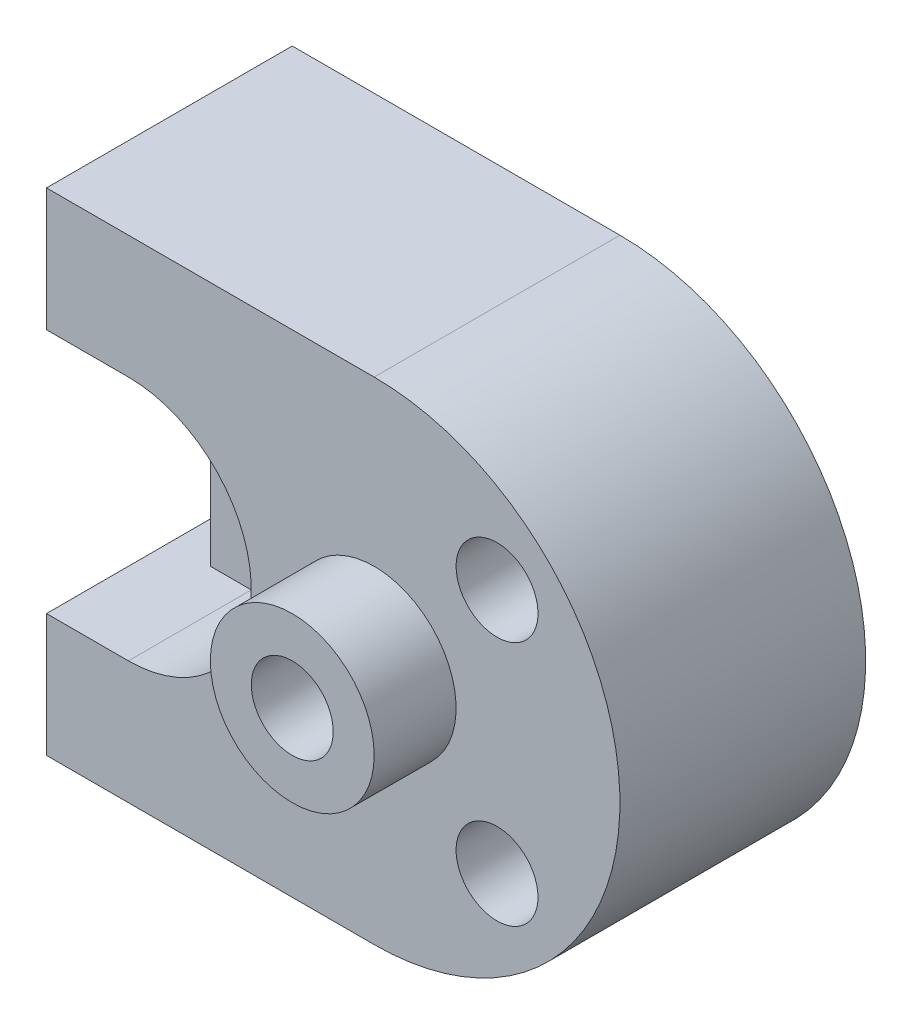
SolidWorks part; units mm, degrees
ref_plane "Front Plane" through (0, 0, 0) normal (0, 0, 1) x (1, 0, 0)
ref_plane "Top Plane" through (0, 0, 0) normal (0, 1, 0) x (1, 0, 0)
ref_plane "Right Plane" through (0, 0, 0) normal (1, 0, 0) x (0, 0, -1)
sketch "Sketch1" plane through (0, 0, 0) normal (0, 0, 1) x (1, 0, 0)
  line L1 (0, 0) -> (140, 0)
  line L2 (0, 0) -> (0, 120)
  line L3 (0, 120) -> (140, 120)
  line L4 (140, 0) -> (140, 120)
  dimension "D1" = 140
  dimension "D2" = 120
extrude "Boss-Extrude1" add sketch "Sketch1" along normal blind 60
sketch "Sketch2" plane through (0, 0, 60) normal (0, 0, 1) x (1, 0, 0)
  line L0 (0, 120) -> (0, 0) construction
  line L1 (0, 90) -> (10, 90)
  line L2 (0, 90) -> (0, 30)
  line L3 (0, 30) -> (10, 30)
  line L4 (10, 90) -> (10, 30)
  line L5 (140, 120) -> (0, 120) construction
  line L6 (80, 120) -> (140, 120)
  line L7 (140, 120) -> (140, 0)
  line L8 (140, 0) -> (80, 0)
  arc A0 (80, 120) -> (80, 0) centre (80, 60) cw
  line M2 (0, 0) -> (140, 0)
  line M3 (140, 0) -> (140, 120)
  line M4 (140, 120) -> (0, 120)
  dimension "D4" = 60
  dimension "D1" = 10
  dimension "D2" = 30
  dimension "D3" = 30
  dimension "D5" = 60
  dimension "D6" = 60
extrude "Cut-Extrude1" cut sketch "Sketch2" against normal blind 60 contours A0 L7 M4 | A0 M3 M2 | L2 L3 L4 L1
ref_plane "Plane1" through (0, 0, 30) normal (0, 0, 1) x (1, 0, 0)
sketch "Sketch3" plane through (0, 0, 30) normal (0, 0, 1) x (1, 0, 0)
  line L0 (10, 90) -> (20, 90)
  line L1 (10, 30) -> (20, 30)
  line L2 (10, 90) -> (10, 30)
  arc A0 (20, 90) -> (20, 30) centre (20, 60) cw
  dimension "D1" = 30
  dimension "D2" = 10
  dimension "D3" = 10
  dimension "D4" = 0
  dimension "D5" = 0
  dimension "D6" = 0
  dimension "D7" = 0
extrude "Cut-Extrude2" cut sketch "Sketch3" along normal blind 60 contours A0 L0 L2 L1
sketch "Sketch4" plane through (0, 0, 30) normal (0, 0, 1) x (1, 0, 0)
  line L0 (0, 30) -> (20, 30) construction
  circle A0 centre (30, 60) radius 10
  point P2 (10, 30)
  dimension "D1" = 20
  dimension "D2" = 30
  dimension "D3" = 20
extrude "Cut-Extrude3" cut sketch "Sketch4" against normal blind 60
ref_plane "Plane2" through (0, 0, 20) normal (0, 0, 1) x (1, 0, 0)
sketch "Sketch5" plane through (0, 0, 20) normal (0, 0, 1) x (1, 0, 0)
  circle A0 centre (110, 90) radius 10
  dimension "D1" = 20
  dimension "D2" = 30
  dimension "D3" = 30
extrude "Cut-Extrude4" cut sketch "Sketch5" against normal blind 60
ref_plane "Plane3" through (0, 0, 40) normal (0, 0, 1) x (1, 0, 0)
sketch "Sketch6" plane through (0, 0, 40) normal (0, 0, 1) x (1, 0, 0)
  circle A0 centre (110, 90) radius 10
  dimension "D1" = 20
  dimension "D2" = 30
  dimension "D3" = 30
extrude "Cut-Extrude5" cut sketch "Sketch6" along normal blind 60
sketch "Sketch7" plane through (0, 0, 40) normal (0, 0, 1) x (1, 0, 0)
  circle A0 centre (110, 90) radius 5
  dimension "D1" = 10
extrude "Cut-Extrude6" cut sketch "Sketch7" against normal blind 60
sketch "Sketch8" plane through (0, 0, 60) normal (0, 0, 1) x (1, 0, 0)
  circle A0 centre (110, 30) radius 10
  dimension "D1" = 20
  dimension "D3" = 30
  dimension "D2" = 30
extrude "Cut-Extrude7" cut sketch "Sketch8" against normal blind 20
sketch "Sketch9" plane through (0, 0, 40) normal (0, 0, 1) x (1, 0, 0)
  circle A0 centre (110, 30) radius 5
  dimension "D1" = 10
extrude "Cut-Extrude8" cut sketch "Sketch9" against normal blind 47
sketch "Sketch10" plane through (0, 0, 0) normal (0, 0, -1) x (-1, 0, 0)
  circle A0 centre (-110, 30) radius 10
  dimension "D1" = 20
extrude "Cut-Extrude9" cut sketch "Sketch10" against normal blind 20
sketch "Sketch11" plane through (0, 0, 60) normal (0, 0, 1) x (1, 0, 0)
  circle A0 centre (80, 60) radius 20
  circle A1 centre (30, 60) radius 10 construction
  dimension "D1" = 40
  dimension "D2" = 80
  dimension "D3" = 0
extrude "Boss-Extrude2" add sketch "Sketch11" along normal blind 20
sketch "Sketch12" plane through (0, 0, 80) normal (0, 0, 1) x (1, 0, 0)
  point P0 (80, 60)
hole_wizard "Ø20.0mm Dowel Hole1" positions "3DSketch1" profile "Sketch13" hole size "Ø20.0" standard "ISO"
sketch3d "3DSketch1"
  point P0 (80, 60, 80)
sketch "Sketch13" plane through (80, 60, 80) normal (1, 0, 0) x (0, -1, 0)
  line L0 (0, 0) -> (0, 36.0086)
  line L1 (0, 36.0086) -> (10, 30)
  line L2 (10, 30) -> (10, 0)
  line L5 (10, 0) -> (0, 0)
  line L10 (0, 36.0086) -> (-10, 30) construction
  line L11 (0, -6.35) -> (0, 107.95) construction
  dimension "Hole Dia." = 20
  dimension "Hole Depth" = 30
  dimension "Drill Angle" = 118
